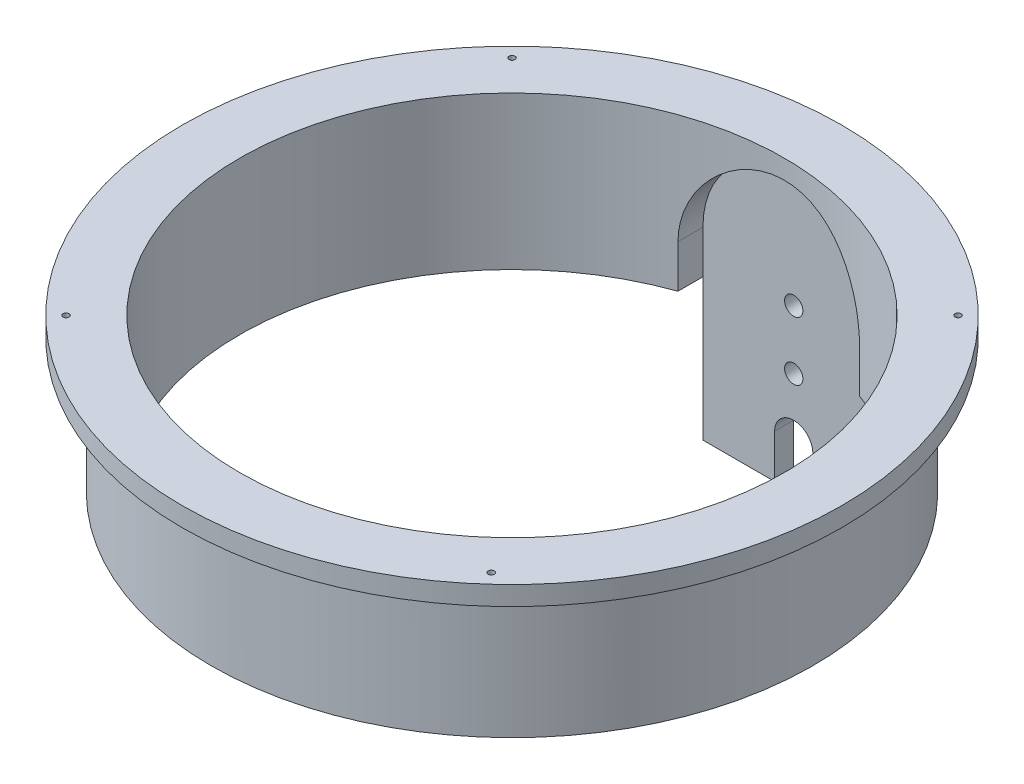
SolidWorks part; units mm, degrees
ref_plane "Front Plane" through (0, 0, 0) normal (0, 0, 1) x (1, 0, 0)
ref_plane "Top Plane" through (0, 0, 0) normal (0, 1, 0) x (1, 0, 0)
ref_plane "Right Plane" through (0, 0, 0) normal (1, 0, 0) x (0, 0, -1)
sketch "Sketch2" plane through (0, 0, 0) normal (0, 0, 1) x (1, 0, 0)
  line L0 (-45.2437, 0) -> (45.2437, 0) construction
  line L1 (0, 12.7) -> (0, -12.7) construction
  line L3 (45.2437, -12.7) -> (50.0063, -12.7)
  line L4 (45.2437, -12.7) -> (45.2437, 12.7)
  line L5 (45.2437, 12.7) -> (50.0063, 12.7)
  line L6 (50.0063, -12.7) -> (50.0063, 9.525)
  line L7 (50.0063, 12.7) -> (54.7687, 12.7)
  line L9 (50.0063, 9.525) -> (54.7687, 9.525)
  line L10 (54.7687, 12.7) -> (54.7687, 9.525)
  point P3 (0, 0)
  point P13 (45.2437, 0)
  point P14 (0, 12.7)
  point P15 (0, -12.7)
  dimension "D1" = 90.4875
  dimension "D2" = 25.4
  dimension "D3" = 4.7625
  dimension "D4" = 3.175
  dimension "D5" = 9.525
revolve "Revolve1" add sketch "Sketch2" angle 360 about L1
sketch "Sketch3" plane through (0, 0, 0) normal (0, 0, 1) x (1, 0, 0)
  line L0 (-15.0812, -12.7) -> (15.0812, -12.7)
  line L1 (0, -12.7) -> (0, 12.7) construction
  line L2 (-15.0812, -12.7) -> (-15.0813, -5.5563)
  line L3 (15.0813, -5.5562) -> (15.0812, -12.7)
  line L4 (54.7687, 12.7) -> (-54.7687, 12.7) construction
  arc A0 (-15.0813, -5.5563) -> (15.0813, -5.5562) centre (0, -5.5563) cw
  point P2 (0, 0)
  point P5 (0, -12.7)
  point P10 (0, 0)
  point P11 (0, 9.525)
  point P12 (15.0812, -12.4272)
  point P13 (0, 0)
  dimension "D3" = 12.7
  dimension "D1" = 30.1625
  dimension "D2" = 3.175
extrude "Cut-Extrude1" cut sketch "Sketch3" against normal blind 1.5875 and the other way blind 3.302 from offset 45.212 offset against normal yes
sketch "Sketch4" plane through (0, 0, -46.7995) normal (0, 0, 1) x (1, 0, 0)
  line L0 (-19.9857, -12.7) -> (19.3127, -12.7) construction
  line L1 (-50.0063, -12.7) -> (50.0063, -12.7) construction
  line L3 (-15.0813, -5.5563) -> (-15.0813, -12.7)
  line L4 (-15.0813, -12.7) -> (15.0812, -12.7)
  line L5 (15.0812, -12.7) -> (15.0813, -5.5562)
  line L6 (-15.0813, -5.5563) -> (-15.0813, -12.7)
  line L7 (-15.0813, -12.7) -> (15.0812, -12.7)
  line L8 (15.0812, -12.7) -> (15.0813, -5.5562)
  line L9 (-15.0813, -12.7) -> (15.0812, -12.7)
  line L10 (-15.0813, -12.7) -> (-15.0812, -36.195)
  line L11 (-15.0812, -36.195) -> (15.0813, -36.195)
  line L12 (15.0812, -12.7) -> (15.0813, -36.195)
  arc A1 (15.0813, -5.5562) -> (-15.0813, -5.5563) centre (0, -5.5563) ccw
  arc A2 (15.0813, -5.5562) -> (-15.0813, -5.5563) centre (0, -5.5563) ccw
  point P11 (0, 9.525)
  point P12 (0, -36.195)
  line M9 (-15.0813, -5.5563) -> (-15.0813, -12.7)
  line M10 (-15.0813, -12.7) -> (15.0812, -12.7)
  line M11 (15.0812, -12.7) -> (15.0813, -5.5562)
  arc M12 (15.0813, -5.5562) -> (-15.0813, -5.5563) centre (0, -5.5563) ccw
  dimension "D2" = 45.72
  dimension "D1" = 0
extrude "Boss-Extrude1" add sketch "Sketch4" against normal blind 3.175 contours M12 M9 M10 M11 | L12 L10 L11 M10
sketch "Sketch5" plane through (0, 0, -46.7995) normal (0, 0, 1) x (1, 0, 0)
  line L0 (0, -36.195) -> (0, 0) construction
  line L1 (-15.0812, -36.195) -> (15.0813, -36.195) construction
  line L2 (0, -36.195) -> (0, -28.9687) construction
  line L3 (-3.175, -36.195) -> (-3.175, -28.9687)
  line L4 (3.175, -36.195) -> (3.175, -28.9687)
  line L5 (-3.175, -36.195) -> (3.175, -36.195)
  circle A0 centre (0, -19.0881) radius 1.524
  circle A1 centre (0, -9.3091) radius 1.524
  arc A2 (3.175, -28.9687) -> (-3.175, -28.9687) centre (0, -28.9687) ccw
  point P2 (0, -19.0881)
  point P3 (0, -9.3091)
  point P9 (0, -36.195)
  point P21 (0, 0)
  point P22 (0, -45.4784)
  point P23 (0, 0)
  dimension "D3" = 3.048
  dimension "D4" = 3.048
  dimension "D7" = 3.175
  dimension "D1" = 17.1069
  dimension "D2" = 26.8859
  dimension "D5" = 6.35
  dimension "D6" = 7.2263
extrude "Cut-Extrude2" cut sketch "Sketch5" against normal through all
sketch "Sketch6" plane through (0, 9.525, 0) normal (0, -1, 0) x (-1, 0, 0)
sketch "Sketch8" plane through (0, 9.525, 0) normal (0, -1, 0) x (-1, 0, 0)
  line L0 (-38.7274, 38.7274) -> (38.7274, -38.7274) construction
  line L2 (-54.7687, 0) -> (54.7687, 0) construction
  line L4 (0, -50.0063) -> (0, -54.7687) construction
  circle A0 centre (0, 0) radius 54.7687 construction
  circle A1 centre (0, 0) radius 52.3875 construction
  arc A2 (-15.0813, 47.6779) -> (15.0813, 47.6779) centre (0, 0) ccw construction
  point P24 (0, -52.3875)
  point P25 (-37.0436, 37.0436)
  point P27 (37.0436, 37.0436)
  point P29 (37.0436, -37.0436)
  point P31 (-35.2795, -38.7274)
  dimension "D1" = 45
hole_wizard "Ø1.0mm Dowel Hole1" positions "Sketch8" profile "Sketch9" hole size "Ø1.0" standard "ANSI Metric" end condition up to next
sketch "Sketch9" plane through (35.2795, 9.525, 38.7274) normal (1, 0, 0) x (0, 0, -1)
  line L0 (0, 0) -> (0, 3.175)
  line L1 (0, 3.175) -> (0.5, 3.175)
  line L2 (0.5, 3.175) -> (0.5, 0)
  line L5 (0.5, 0) -> (0, 0)
  line L11 (0, -6.35) -> (0, 107.95) construction
  dimension "Thru Hole Dia." = 1
  dimension "Thru Hole Depth" = 3.175
